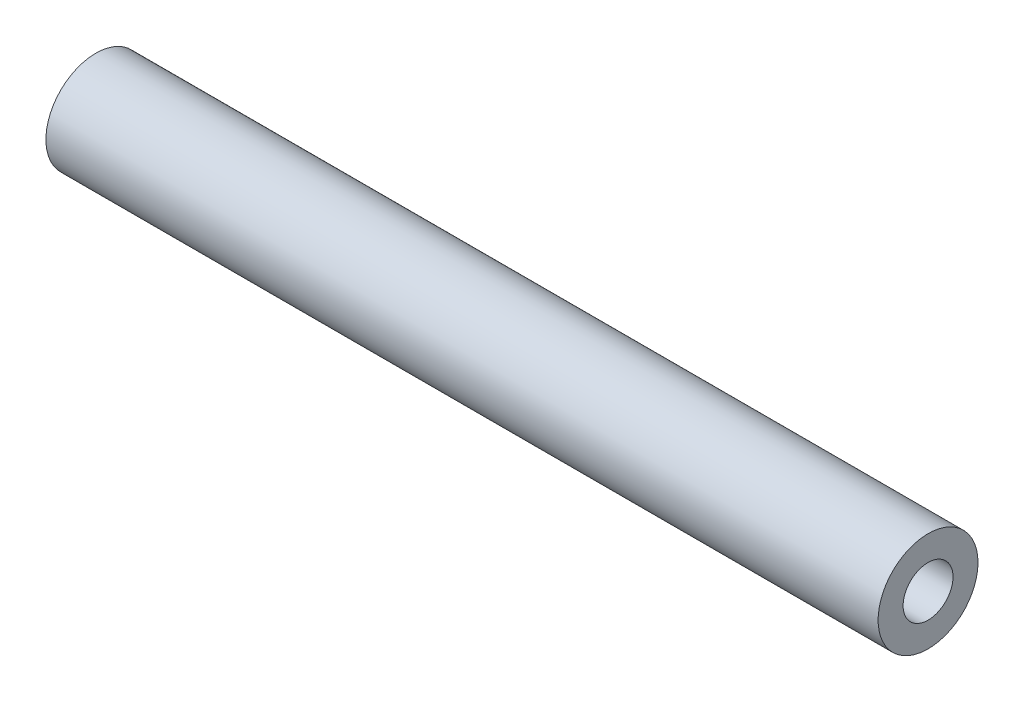
SolidWorks part; units mm, degrees
ref_plane "Front Plane" through (0, 0, 0) normal (0, 0, 1) x (1, 0, 0)
ref_plane "Top Plane" through (0, 0, 0) normal (0, 1, 0) x (1, 0, 0)
ref_plane "Right Plane" through (0, 0, 0) normal (1, 0, 0) x (0, 0, -1)
sketch "Sketch1" plane through (0, 0, 0) normal (1, 0, 0) x (0, 0, -1)
  circle A0 centre (0, 0) radius 6
extrude "Boss-Extrude1" add sketch "Sketch1" along normal blind 100
sketch "Sketch2" plane through (100, 0, 0) normal (1, 0, 0) x (0, 0, -1)
  circle A0 centre (0, 0) radius 3
extrude "Cut-Extrude1" cut sketch "Sketch2" against normal blind 30
sketch "Sketch3" plane through (0, 0, 0) normal (-1, 0, 0) x (0, 0, 1)
  circle A0 centre (0, 0) radius 3
extrude "Cut-Extrude2" cut sketch "Sketch3" against normal blind 60
